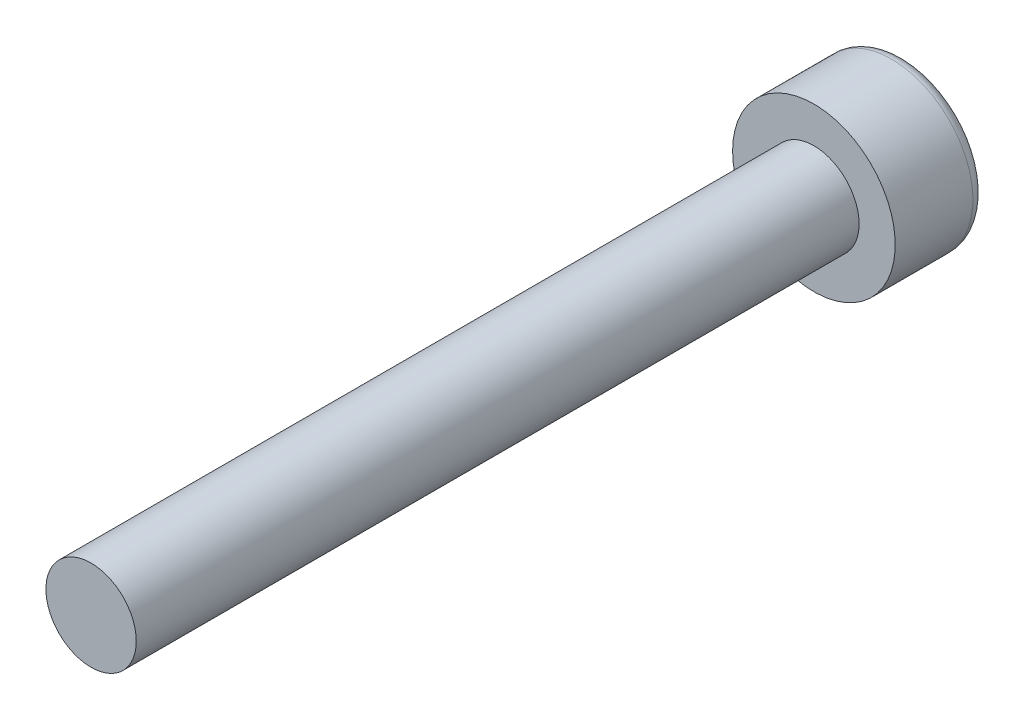
SolidWorks part; units mm, degrees
material "Acero aleado"
ref_plane "Alzado" through (0, 0, 0) normal (0, 0, 1) x (1, 0, 0)
ref_plane "Planta" through (0, 0, 0) normal (0, 1, 0) x (1, 0, 0)
ref_plane "Vista lateral" through (0, 0, 0) normal (1, 0, 0) x (0, 0, -1)
sketch "Croquis1" plane through (0, 0, 0) normal (0, 0, 1) x (1, 0, 0)
  circle A0 centre (0, 0) radius 1.25
  dimension "D1" = 2.5
extrude "Saliente-Extruir1" add sketch "Croquis1" along normal blind 20
sketch "Croquis2" plane through (0, 0, 0) normal (0, 0, -1) x (-1, 0, 0)
  circle A0 centre (0, 0) radius 2.25
  dimension "D1" = 4.5
extrude "Saliente-Extruir2" add sketch "Croquis2" along normal blind 2.5
sketch "Croquis3" plane through (0, 0, -2.5) normal (0, 0, -1) x (-1, 0, 0)
  line L1 (0, -1.1547) -> (1, -0.5774)
  line L2 (1, -0.5774) -> (1, 0.5774)
  line L3 (1, 0.5774) -> (0, 1.1547)
  line L4 (0, 1.1547) -> (-1, 0.5774)
  line L5 (-1, 0.5774) -> (-1, -0.5774)
  line L6 (-1, -0.5774) -> (0, -1.1547)
  circle A0 centre (0, 0) radius 1 construction
  dimension "D1" = 2
extrude "Cortar-Extruir1" cut sketch "Croquis3" against normal blind 1.5
fillet "Redondeo1" radius 0.35 1 edges at (-2.25, 0, -2.5)
